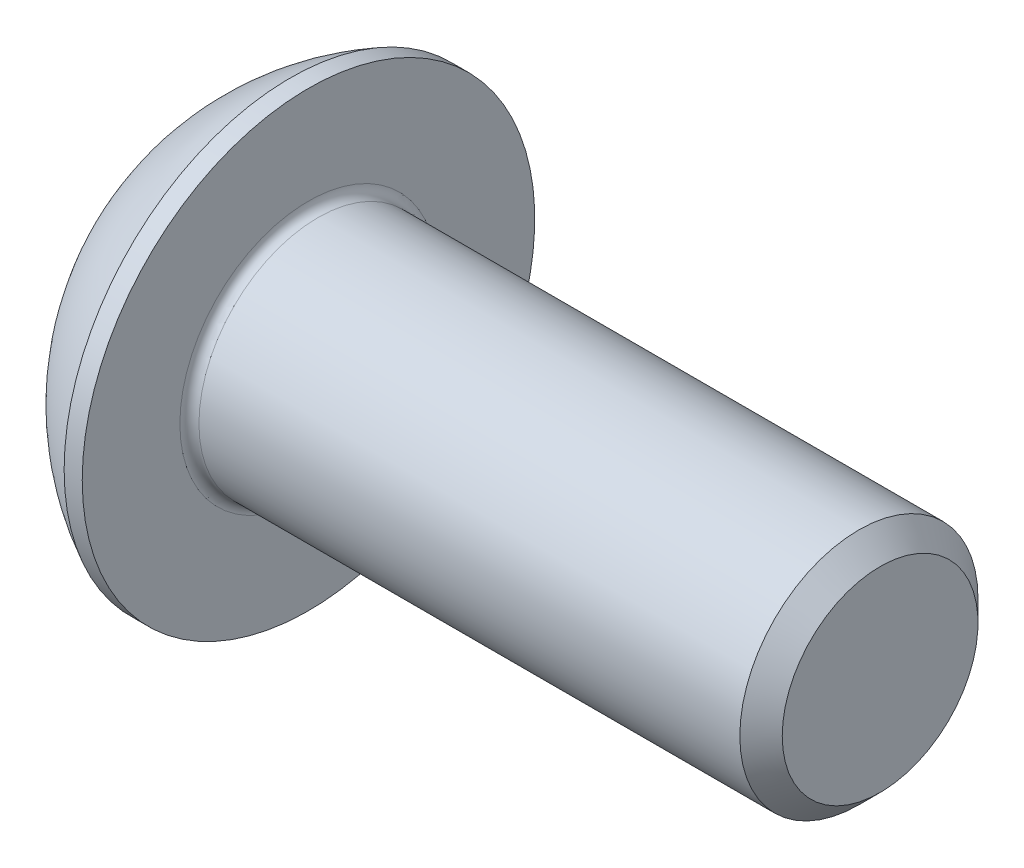
SolidWorks part; units mm, degrees
ref_plane "Plane1" through (0, 0, 0) normal (0, 0, 1) x (1, 0, 0)
ref_plane "Plane2" through (0, 0, 0) normal (0, 1, 0) x (1, 0, 0)
ref_plane "Plane3" through (0, 0, 0) normal (1, 0, 0) x (0, 0, -1)
sketch "BodySke" plane through (0, 0, 0) normal (0, 0, 1) x (1, 0, 0)
  line L0 (14.75, 0) -> (14.75, 2.055)
  line L1 (14.305, 2.5) -> (2.75, 2.5)
  line L2 (2.75, 2.5) -> (2.75, 4.75)
  line L3 (2.75, 4.75) -> (2.37, 4.75)
  line L4 (0, 0) -> (101.6, 0) construction
  line L5 (2.75, -4.75) -> (2.37, -4.75) construction
  line L6 (55.6768, -2.5) -> (2.75, -2.5) construction
  line L7 (14.75, 0) -> (0, 0)
  line L8 (0, 2.375) -> (0, -2.375) construction
  line L9 (0, 0) -> (0, 2.375)
  line L10 (14.75, 2.055) -> (14.305, 2.5)
  line L11 (14.75, -2.055) -> (14.305, -2.5) construction
  line L12 (3.55, 9.525) -> (3.55, -2.5) construction
  line L13 (2.75, 9.525) -> (2.75, -2.5) construction
  arc A1 (0, 2.375) -> (2.37, 4.75) centre (4.755, 0) cw
  dimension "Diameter" = 5
  dimension "Length" = 12
  dimension "Head_dia" = 9.5
  dimension "D1" = 4.75
  dimension "Head_ht" = 2.75
  dimension "Head_side_ht" = 0.38
  dimension "Minor_dia" = 4.11
  dimension "Body_ch_ang" = 45
  dimension "Advance" = 0.8
  dimension "Thread_nom" = 12
revolve "BaseBody" add sketch "BodySke" angle 360 about L4
cosmetic thread "ThreadCosmetic" [suppressed] parameters "Thread_length"=10.4, "Thread_minor"=4.11
fillet "Fillet1" radius 0.2 1 edges at (2.75, 0, 2.5)
sketch "Sketch2" plane through (0, 0, 0) normal (0, 0, 1) x (1, 0, 0)
  line L0 (0, 1.5) -> (1.56, 1.5)
  line L1 (1.56, 1.5) -> (2.426, 0)
  line L3 (2.426, 0) -> (0, 0)
  line L4 (0, 0) -> (0, 1.5)
  line L5 (0, -1.5) -> (1.56, -1.5) construction
  line L6 (0, 0) -> (47.625, 0) construction
  dimension "D2" = 60
  dimension "PreBroach_depth" = 1.56
  dimension "PreBroach_dia" = 3
revolve "PreBroach" cut sketch "Sketch2" angle 360 about L6
sketch "Sketch3" plane through (0, 0, 0) normal (1, 0, 0) x (0, 0, -1)
  line L0 (-1.5, -0.866) -> (-1.5, 0.866)
  line L1 (-1.5, 0.866) -> (0, 1.7321)
  line L2 (0, 1.7321) -> (1.5, 0.866)
  line L3 (1.5, 0.866) -> (1.5, -0.866)
  line L4 (1.5, -0.866) -> (0, -1.7321)
  line L5 (0, -1.7321) -> (-1.5, -0.866)
  dimension "Hex_size" = 3
  dimension "D3" = 3
  dimension "D1" = 1.5
  dimension "D2" = 1.5
extrude "Hex" cut sketch "Sketch3" along normal blind 1.56
sketch "ThdSchSke" plane through (0, 0, 0) normal (0, 0, 1) x (1, 0, 0)
  line L0 (4.35, -2.055) -> (4.0384, -2.5)
  line L1 (4.35, -2.055) -> (4.6616, -2.5)
  line L2 (4.6616, -2.5) -> (4.6616, -3.125)
  line L3 (-3.175, 0) -> (5.1513, 0) construction
  line L5 (4.6616, -3.125) -> (4.0384, -3.125)
  line L6 (4.0384, -3.125) -> (4.0384, -2.5)
  dimension "Diameter" = 5
  dimension "Thread_minor" = 4.11
  dimension "SideAngle" = 55
  dimension "VeeAngle" = 70
  dimension "Overcut" = 6.25
  dimension "Start" = 4.35
revolve "ThreadSchematic" [suppressed] cut sketch "ThdSchSke" angle 360 about L3
pattern_linear "ThdSchPat" [suppressed]
equation "\"D1@BodySke\" = \"Head_dia@BodySke\" * .5"
equation "\"Thread_minor@ThreadCosmetic\" = \"Minor_dia@BodySke\""
equation "\"D1@Sketch3\" = \"Hex_size@Sketch3\" / 2"
equation "\"D2@Sketch3\" = \"D1@Sketch3\""
equation "\"D3@Sketch3\" = \"Hex_size@Sketch3\""
equation "\"Thread_length@ThreadCosmetic\" = ((sgn( (\"Length@BodySke\" - \"Advance@BodySke\" * 2.0) - \"Thread_nom@BodySke\" )-1)*( (\"Length@BodySke\" - \"Advance@BodySke\" * 2.0) - \"Thread_nom@BodySke\" ))/-2+ \"Thread_nom@BodySke\""
equation "\"Thread_minor@ThdSchSke\" = \"Minor_dia@BodySke\""
equation "\"Diameter@ThdSchSke\" = \"Diameter@BodySke\""
equation "\"Overcut@ThdSchSke\" = \"Diameter@BodySke\" * 1.25"
equation "\"Start@ThdSchSke\" = \"Head_ht@BodySke\" + \"Length@BodySke\" - \"Thread_length@ThreadCosmetic\"  '---Non-countersunk---"
equation "\"Num_threads@ThdSchPat\" = int( \"Thread_length@ThreadCosmetic\" / \"Advance@BodySke\" + 0.999 )  + 1"
equation "\"Advance@ThdSchPat\" = \"Thread_length@ThreadCosmetic\" /  (\"Num_threads@ThdSchPat\" - 1) 'relax it"
equation "\"Num_threads@ThdSchPat\" = \"Num_threads@ThdSchPat\" - sgn( \"Num_threads@ThdSchPat\" - 1) '---chamfered tips only---"
